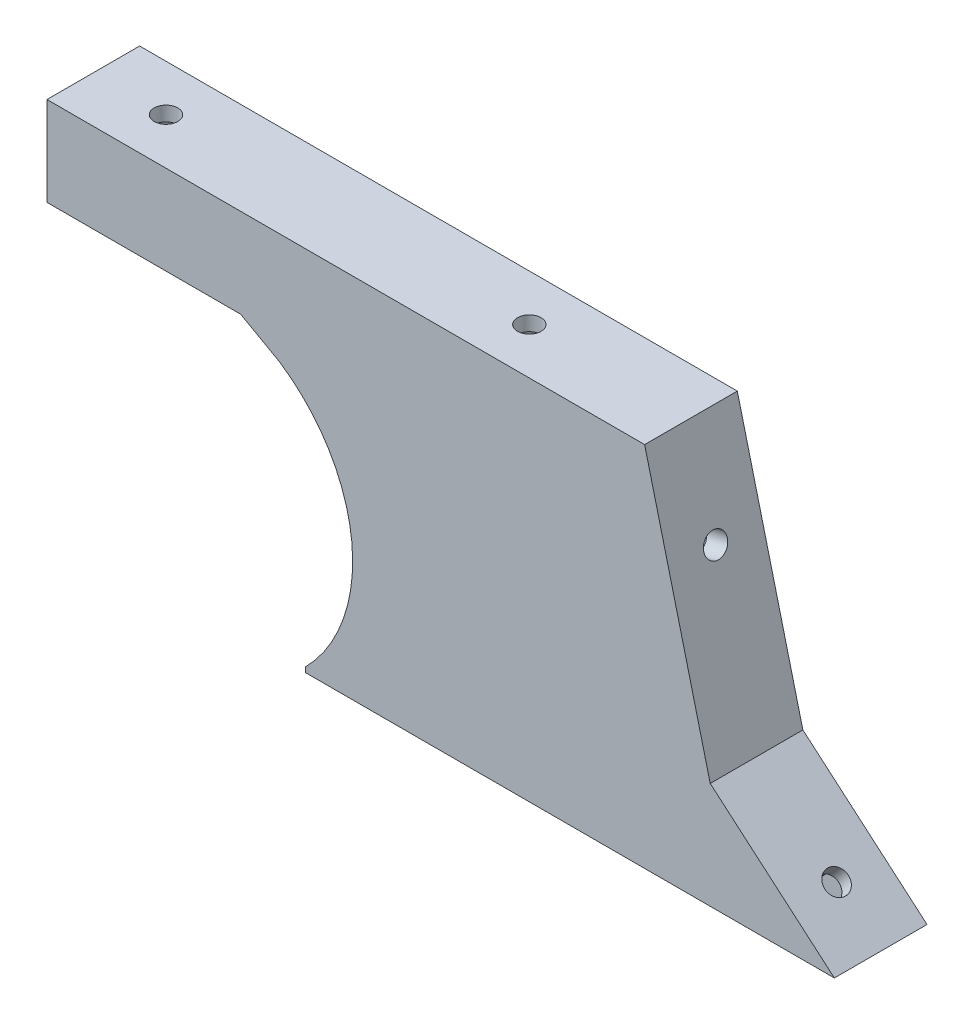
SolidWorks part; units mm, degrees
ref_plane "Alzado" through (0, 0, 0) normal (0, 0, 1) x (1, 0, 0)
ref_plane "Planta" through (0, 0, 0) normal (0, 1, 0) x (1, 0, 0)
ref_plane "Vista lateral" through (0, 0, 0) normal (1, 0, 0) x (0, 0, -1)
sketch "Croquis1" plane through (0, 0, 0) normal (0, 0, 1) x (1, 0, 0)
  line L0 (0, 0.6807) -> (0, 0)
  line L1 (0, 0) -> (72.7832, 0)
  line L2 (72.7832, 0) -> (55.7, 14.6421)
  line L3 (55.7, 14.6421) -> (46.6759, 50.5119)
  line L4 (46.6759, 50.5119) -> (-35.5627, 50.5119)
  line L5 (-35.5627, 50.5119) -> (-35.5627, 38.25)
  line L6 (-35.5627, 38.25) -> (-8.9133, 38.25)
  line L7 (-8.9133, 38.25) -> (-3.5627, 35.25)
  arc A0 (-3.5627, 35.25) -> (0, 0.6807) centre (-16, 16.5) cw
  dimension "D1" = 22.5
extrude "Saliente-Extruir1" add sketch "Croquis1" against normal blind 3
sketch "Croquis5" plane through (0, 0, -3) normal (0, 0, -1) x (-1, 0, 0)
  line L0 (35.5627, 50.5119) -> (35.5627, 38.25) construction
  line L2 (-46.6759, 50.5119) -> (35.5627, 50.5119) construction
  line L5 (-51.239, 11.8804) -> (-59.2664, 5)
  line L7 (-51.239, 11.8804) -> (-42.5264, 46.5119)
  line L9 (35.5627, 38.25) -> (8.9133, 38.25) construction
  line L11 (35.5627, 50.5119) -> (35.5627, 38.25)
  line L12 (35.5627, 38.25) -> (31.5627, 38.25)
  line L14 (31.5627, 46.5119) -> (31.5627, 38.25)
  line L16 (31.5627, 46.5119) -> (-42.5264, 46.5119)
  line L19 (0, 0.6807) -> (0, 0)
  line L20 (-3.3391, 5) -> (-59.2664, 5)
  line L21 (0, 0) -> (-72.7832, 0)
  line L22 (-72.7832, 0) -> (-55.7, 14.6421)
  line L23 (-55.7, 14.6421) -> (-46.6759, 50.5119)
  line L24 (-46.6759, 50.5119) -> (35.5627, 50.5119)
  arc A0 (3.5627, 35.25) -> (0, 0.6807) centre (16, 16.5) ccw construction
  arc A1 (-3.3391, 5) -> (0, 0.6807) centre (16, 16.5) ccw
  dimension "D1" = 4
  dimension "D2" = 38.9017
  dimension "D3" = 78.0891
  dimension "D4" = 86.8016
  dimension "D5" = 94.8291
  dimension "D6" = 4
extrude "Saliente-Extruir2" add sketch "Croquis5" along normal blind 9.75
sketch "Croquis6" plane through (0, 0, 0) normal (0, -1, 0) x (1, 0, 0)
  circle A0 centre (7, -7) radius 1.625
  circle A1 centre (52.7832, -7) radius 1.625
  dimension "D1" = 3.25
ref_plane "Plano1" through (3.3391, 5, -12.75) normal (0, 0, 1) x (1, 0, 0)
extrude "Cortar-Extruir1" cut sketch "Croquis6" against normal up to vertex (5 mm away)
sketch "Croquis8" plane through (0, 5, 0) normal (0, 1, 0) x (1, 0, 0)
  line L1 (3.82, 7) -> (5.41, 4.246)
  line L2 (5.41, 4.246) -> (8.59, 4.246)
  line L3 (8.59, 4.246) -> (10.18, 7)
  line L4 (10.18, 7) -> (8.59, 9.754)
  line L5 (8.59, 9.754) -> (5.41, 9.754)
  line L6 (5.41, 9.754) -> (3.82, 7)
  line L7 (49.6032, 7) -> (51.1932, 4.246)
  line L8 (51.1932, 4.246) -> (54.3732, 4.246)
  line L9 (54.3732, 4.246) -> (55.9632, 7)
  line L10 (55.9632, 7) -> (54.3732, 9.754)
  line L11 (54.3732, 9.754) -> (51.1932, 9.754)
  line L12 (51.1932, 9.754) -> (49.6032, 7)
  circle A0 centre (7, 7) radius 2.754 construction
  circle A1 centre (52.7832, 7) radius 2.754 construction
  dimension "D1" = 5.5079
extrude "Cortar-Extruir2" cut sketch "Croquis8" against normal blind 2
sketch "Croquis9" plane through (30.8242, 35.9632, 0) normal (0.6508, 0.7593, 0) x (0.7593, -0.6508, 0)
  line L1 (55.2622, 0) -> (32.7627, 0) construction
  line L2 (55.2622, 6.375) -> (32.7627, 6.375) construction
  line L3 (55.2622, 12.75) -> (55.2622, 0) construction
  line L4 (32.7627, 12.75) -> (32.7627, 0) construction
  line L5 (47.2622, 0) -> (47.2622, 12.75) construction
  line L6 (50.4422, 6.375) -> (48.8522, 9.129)
  line L7 (48.8522, 9.129) -> (45.6722, 9.129)
  line L8 (45.6722, 9.129) -> (44.0822, 6.375)
  line L9 (44.0822, 6.375) -> (45.6722, 3.621)
  line L10 (45.6722, 3.621) -> (48.8522, 3.621)
  line L11 (48.8522, 3.621) -> (50.4422, 6.375)
  circle A2 centre (47.2622, 6.375) radius 2.754 construction
  dimension "D2" = 5.5079
extrude "Cortar-Extruir4" cut sketch "Croquis9" against normal blind 10
sketch "Croquis10" plane through (30.8242, 35.9632, 0) normal (0.6508, 0.7593, 0) x (0.7593, -0.6508, 0)
  line L0 (50.4422, 6.375) -> (44.0822, 6.375) construction
  line L2 (50.4422, 6.375) -> (48.8522, 9.129)
  line L3 (48.8522, 9.129) -> (45.6722, 9.129)
  line L4 (45.6722, 9.129) -> (44.0822, 6.375)
  line L5 (44.0822, 6.375) -> (45.6722, 3.621)
  line L6 (45.6722, 3.621) -> (48.8522, 3.621)
  line L7 (48.8522, 3.621) -> (50.4422, 6.375)
  circle A0 centre (47.2622, 6.375) radius 1.625
  circle A1 centre (47.2622, 6.375) radius 2.754 construction
  dimension "D1" = 3.25
extrude "Saliente-Extruir3" add sketch "Croquis10" against normal blind 2
sketch "Croquis12" plane through (55.8489, 14.0503, 0) normal (0.9698, 0.244, 0) x (0, 0, -1)
  line L0 (6.375, 19.104) -> (6.375, 28.3508) construction
  line L4 (187, 23.7274) -> (0, 23.7274) construction
  line L5 (0, 0.6102) -> (0, 37.5977) construction
  circle A0 centre (188.625, 23.7274) radius 1.625 construction
  circle A1 centre (6.375, 23.7274) radius 1.625
  dimension "D1" = 3.25
  dimension "D2" = 6.375
extrude "Cortar-Extruir5" cut sketch "Croquis12" against normal up to vertex (5 mm away)
sketch "Croquis13" plane through (51, 12.8305, 0) normal (-0.9698, -0.244, 0) x (0, 0, 1)
  line L1 (-6.375, 20.5474) -> (-3.621, 22.1374)
  line L2 (-3.621, 22.1374) -> (-3.621, 25.3174)
  line L3 (-3.621, 25.3174) -> (-6.375, 26.9074)
  line L4 (-6.375, 26.9074) -> (-9.129, 25.3174)
  line L5 (-9.129, 25.3174) -> (-9.129, 22.1374)
  line L6 (-9.129, 22.1374) -> (-6.375, 20.5474)
  circle A0 centre (-6.375, 23.7274) radius 2.754 construction
  dimension "D1" = 5.5079
extrude "Cortar-Extruir6" cut sketch "Croquis13" against normal blind 2
sketch "Croquis14" plane through (0, 50.5119, 0) normal (0, 1, 0) x (1, 0, 0)
  line L1 (46.6759, 0) -> (-35.5627, 0) construction
  line L2 (-25.5627, 0) -> (-25.5627, 12.75) construction
  line L3 (-35.5627, 6.375) -> (46.6759, 6.375) construction
  line L4 (-35.5627, 12.75) -> (-35.5627, 0) construction
  line L5 (46.6759, 12.75) -> (46.6759, 0) construction
  line L6 (24.4373, 0) -> (24.4373, 12.75) construction
  circle A2 centre (-25.5627, 6.375) radius 1.625
  circle A3 centre (24.4373, 6.375) radius 1.625
  dimension "D1" = 3.25
  dimension "D2" = 22.2386
  dimension "D3" = 72.2386
extrude "Cortar-Extruir7" cut sketch "Croquis14" against normal up to vertex (4 mm away)
sketch "Croquis15" plane through (0, 46.5119, 0) normal (0, -1, 0) x (1, 0, 0)
  line L1 (-22.3827, -6.375) -> (-23.9727, -3.621)
  line L2 (-23.9727, -3.621) -> (-27.1527, -3.621)
  line L3 (-27.1527, -3.621) -> (-28.7427, -6.375)
  line L4 (-28.7427, -6.375) -> (-27.1527, -9.129)
  line L5 (-27.1527, -9.129) -> (-23.9727, -9.129)
  line L6 (-23.9727, -9.129) -> (-22.3827, -6.375)
  line L7 (21.2573, -6.375) -> (22.8473, -9.129)
  line L8 (22.8473, -9.129) -> (26.0273, -9.129)
  line L9 (26.0273, -9.129) -> (27.6173, -6.375)
  line L10 (27.6173, -6.375) -> (26.0273, -3.621)
  line L11 (26.0273, -3.621) -> (22.8473, -3.621)
  line L12 (22.8473, -3.621) -> (21.2573, -6.375)
  circle A0 centre (-25.5627, -6.375) radius 2.754 construction
  circle A1 centre (24.4373, -6.375) radius 2.754 construction
  dimension "D1" = 5.5079
extrude "Cortar-Extruir8" cut sketch "Croquis15" against normal blind 2
sketch "Croquis17" plane through (-35.5627, 0, 0) normal (-1, 0, 0) x (0, 0, 1)
  circle A0 centre (-7.9825, 42.38) radius 1.625
  dimension "D1" = 3.25
extrude "Cortar-Extruir9" cut sketch "Croquis17" against normal up to vertex (4 mm away)
sketch "Croquis18" plane through (-31.5627, 0, 0) normal (1, 0, 0) x (0, 0, -1)
  line L1 (7.9825, 39.2) -> (10.7365, 40.79)
  line L2 (10.7365, 40.79) -> (10.7365, 43.97)
  line L3 (10.7365, 43.97) -> (7.9825, 45.56)
  line L4 (7.9825, 45.56) -> (5.2285, 43.97)
  line L5 (5.2285, 43.97) -> (5.2285, 40.79)
  line L6 (5.2285, 40.79) -> (7.9825, 39.2)
  circle A0 centre (7.9825, 42.38) radius 2.754 construction
  dimension "D1" = 5.5079
extrude "Cortar-Extruir10" cut sketch "Croquis18" against normal blind 2
